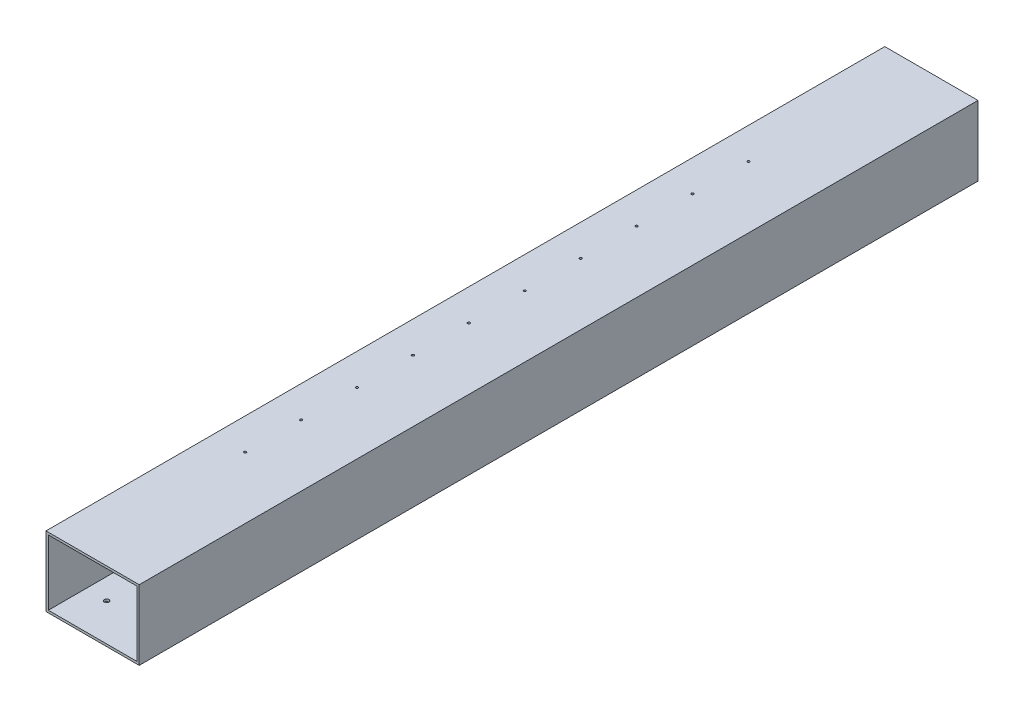
SolidWorks part; units mm, degrees
ref_plane "Front Plane" through (0, 0, 0) normal (0, 0, 1) x (1, 0, 0)
ref_plane "Top Plane" through (0, 0, 0) normal (0, 1, 0) x (1, 0, 0)
ref_plane "Right Plane" through (0, 0, 0) normal (1, 0, 0) x (0, 0, -1)
sketch "Sketch2" plane through (0, 0, 0) normal (0, 0, 1) x (1, 0, 0)
  line L0 (-95, 70) -> (95, 70)
  line L1 (-100, 75) -> (100, 75)
  line L2 (-100, 75) -> (-100, -75)
  line L4 (100, 75) -> (100, -75)
  line L5 (-95, 70) -> (-95, -70)
  line L6 (-95, -70) -> (95, -70)
  line L10 (-95, -70) -> (95, -70) construction
  line L11 (-100, -75) -> (100, -75) construction
  line L12 (-95, 70) -> (-95, -70) construction
  line L13 (95, 70) -> (95, -70) construction
  line L18 (95, -70) -> (95, 70)
  line L19 (-100, -75) -> (100, -75)
  dimension "D1" = 200
  dimension "D2" = 150
  dimension "D3" = 5
extrude "Boss-Extrude1" add sketch "Sketch2" along normal blind 1800
ref_plane "Plane4" through (0, 0, 900) normal (0, 0, 1) x (1, 0, 0)
sketch "Sketch5" plane through (0, 75, 0) normal (0, 1, 0) x (1, 0, 0)
  line L0 (-100, -1800) -> (-100, 0) construction
  line L1 (100, 0) -> (-100, 0) construction
  circle A0 centre (-32.7, -360) radius 2.5
  circle A1 centre (-32.7, -480) radius 2.5
  circle A2 centre (-32.7, -600) radius 2.5
  circle A3 centre (-32.7, -720) radius 2.5
  circle A4 centre (-32.7, -840) radius 2.5
  circle A5 centre (-32.7, -960) radius 2.5
  circle A6 centre (-32.7, -1080) radius 2.5
  circle A7 centre (-32.7, -1200) radius 2.5
  circle A8 centre (-32.7, -1320) radius 2.5
  circle A9 centre (-32.7, -1440) radius 2.5
  dimension "D1" = 5
  dimension "D2" = 67.3
  dimension "D3" = 360
  dimension "D4" = 10
extrude "Cut-Extrude3" cut sketch "Sketch5" against normal blind 10
sketch "Sketch6" plane through (0, -75, 0) normal (0, -1, 0) x (1, 0, 0)
  circle A0 centre (-50, 1720) radius 5
  circle A1 centre (50, 1720) radius 5
  circle A2 centre (50, 1590) radius 5
  circle A3 centre (-50, 1590) radius 5
  circle A4 centre (50, 1412.5) radius 2
  circle A5 centre (50, 1387.5) radius 2
  circle A6 centre (50, 1162.5) radius 2
  circle A7 centre (50, 1137.5) radius 2
  circle A8 centre (50, 912.5) radius 2
  circle A9 centre (50, 887.5) radius 2
  circle A10 centre (50, 662.5) radius 2
  circle A11 centre (50, 637.5) radius 2
  circle A12 centre (50, 412.5) radius 2
  circle A13 centre (50, 387.5) radius 2
  circle A14 centre (-50, 210) radius 5
  circle A15 centre (50, 210) radius 5
  circle A16 centre (50, 80) radius 5
  circle A17 centre (-50, 80) radius 5
  dimension "D1" = 2
  dimension "D2" = 2
extrude "Cut-Extrude4" cut sketch "Sketch6" against normal blind 5
